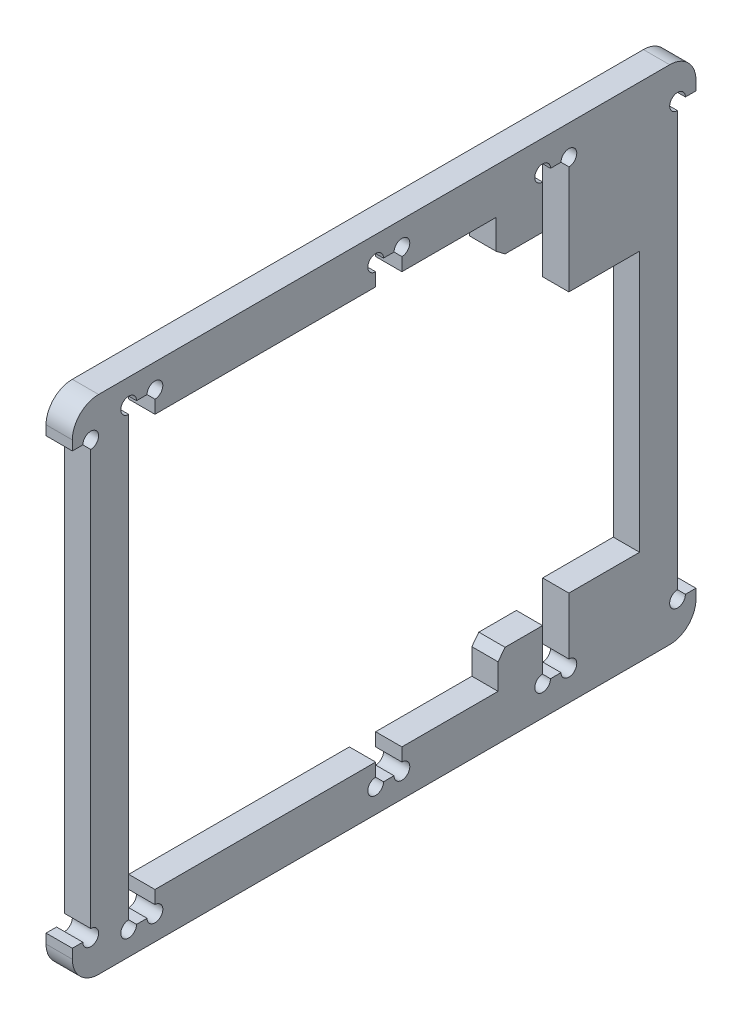
SolidWorks part; units mm, degrees
ref_plane "Front" through (0, 0, 0) normal (0, 0, 1) x (1, 0, 0)
ref_plane "Top" through (0, 0, 0) normal (0, 1, 0) x (1, 0, 0)
ref_plane "Right" through (0, 0, 0) normal (1, 0, 0) x (0, 0, -1)
sketch "Sketch1" plane through (0, 0, 0) normal (1, 0, 0) x (0, 0, -1)
  line L0 (0, 47.8186) -> (0, -47.8186) construction
  line L1 (-59.3692, -47.8186) -> (0, -47.8186)
  line L2 (-59.3692, -47.8186) -> (-59.3692, -41)
  line L3 (-59.3692, 47.8186) -> (59.3692, 47.8186)
  line L4 (59.3692, -47.8186) -> (59.3692, -41)
  line L5 (-59.3692, -47.8186) -> (59.3692, 47.8186) construction
  line L6 (-59.3692, 47.8186) -> (59.3692, -47.8186) construction
  line L7 (-70.2933, 0) -> (70.2933, 0) construction
  line L8 (30.1791, 39.1754) -> (48.6382, 39.1754) construction
  line L9 (30.1791, -39.1754) -> (48.6382, -39.1754) construction
  line L10 (21.7026, -39.1754) -> (21.7026, -34.307)
  line L11 (21.7026, -34.307) -> (23.0249, -32.5698)
  line L12 (23.0249, -32.5698) -> (30.1791, -32.5698)
  line L13 (21.2876, 39.1754) -> (21.2876, 33.6105)
  line L14 (-55.8692, -41) -> (-59.3692, -41)
  line L15 (-55.8692, -41) -> (-55.8692, 41)
  line L16 (0, -47.8186) -> (59.3692, -47.8186)
  line L17 (-55.8692, 41) -> (-59.3692, 41)
  line L18 (-55.8692, -41) -> (-59.3692, 41) construction
  line L19 (-59.3692, -41) -> (-55.8692, 41) construction
  line L20 (59.3692, -41) -> (55.8692, 41) construction
  line L21 (55.8692, -41) -> (59.3692, 41) construction
  line L22 (55.8692, 41) -> (59.3692, 41)
  line L23 (-59.3692, 41) -> (-59.3692, 47.8186)
  line L24 (55.8692, -41) -> (55.8692, 41)
  line L25 (55.8692, -41) -> (59.3692, -41)
  line L26 (59.3692, 41) -> (59.3692, 47.8186)
  line L27 (21.2876, 33.6105) -> (23.0249, 32.2882)
  line L28 (-48.6382, -39.1754) -> (-48.6382, 39.1754)
  line L29 (-48.6382, 39.1754) -> (21.2876, 39.1754)
  line L30 (48.6382, -29.7104) -> (48.6382, 19.9452)
  line L31 (-48.6382, -39.1754) -> (48.6382, 39.1754) construction
  line L32 (-48.6382, 39.1754) -> (48.6382, -39.1754) construction
  line L33 (30.1791, 39.1754) -> (21.2876, 39.1754) construction
  line L34 (35.1791, 19.9452) -> (35.1791, 42.077)
  line L35 (30.1791, 42.077) -> (30.1791, 32.2882)
  line L36 (30.1791, 42.077) -> (35.1791, 42.077)
  line L37 (35.1791, 19.9452) -> (48.6382, 19.9452)
  line L38 (21.7026, -39.1754) -> (-48.6382, -39.1754)
  line L39 (30.1791, -39.1754) -> (21.7026, -39.1754) construction
  line L40 (23.0249, 32.2882) -> (30.1791, 32.2882)
  line L41 (30.1791, -42.077) -> (35.1791, -42.077)
  line L42 (30.1791, -42.077) -> (30.1791, -32.5698)
  line L43 (35.1791, -29.7104) -> (35.1791, -42.077)
  line L44 (35.1791, -29.7104) -> (48.6382, -29.7104)
  line L46 (48.6382, 39.1754) -> (48.6382, 19.9452) construction
  line L47 (48.6382, -29.7104) -> (48.6382, -39.1754) construction
  point P0 (0, 0)
  point P12 (-57.6192, 0)
  point P24 (57.6192, 0)
  point P25 (0, 0)
  dimension "D1" = 3.5
  dimension "D2" = 82
  dimension "D3" = 5
extrude "Boss-Extrude1" add sketch "Sketch1" along normal blind 5
fillet "Fillet1" radius 5 4 edges at (2.5, 47.8186, 59.3692) (2.5, -47.8186, 59.3692) (2.5, -47.8186, -59.3692) (2.5, 47.8186, -59.3692)
sketch "Sketch2" plane through (0, 0, 0) normal (-1, 0, 0) x (0, 0, 1)
  line L0 (-23.2735, 0) -> (52.259, 0) construction
  line L1 (-3.3843, -43.1754) -> (1.6157, -43.1754)
  line L2 (-3.3843, -43.1754) -> (-3.3843, 43.1754)
  line L3 (-3.3843, 43.1754) -> (1.6157, 43.1754)
  line L4 (1.6157, -43.1754) -> (1.6157, 43.1754)
  line L5 (-3.3843, -43.1754) -> (1.6157, 43.1754) construction
  line L6 (-3.3843, 43.1754) -> (1.6157, -43.1754) construction
  line L7 (-21.2876, 39.1754) -> (48.6382, 39.1754) construction
  line L8 (43.6382, -43.1754) -> (48.6382, -43.1754)
  line L9 (43.6382, -43.1754) -> (43.6382, 43.1754)
  line L10 (43.6382, 43.1754) -> (48.6382, 43.1754)
  line L11 (48.6382, -43.1754) -> (48.6382, 43.1754)
  line L12 (43.6382, -43.1754) -> (48.6382, 43.1754) construction
  line L13 (43.6382, 43.1754) -> (48.6382, -43.1754) construction
  line L15 (48.6382, 39.1754) -> (48.6382, -39.1754) construction
  point P0 (-0.8843, 0)
  point P8 (46.1382, 0)
  line M18 (48.6382, -39.1754) -> (-21.7026, -39.1754)
  line M30 (-21.2876, 39.1754) -> (48.6382, 39.1754)
  dimension "D1" = 4
  dimension "D2" = 5
extrude "Cut-Extrude1" cut sketch "Sketch2" against normal up to next contours L11 L10 L9 M30 | L8 L11 L9 M18 | L1 L4 L2 M18 | L4 L3 L2 M30
sketch "Sketch3" plane through (0, 0, 0) normal (-1, 0, 0) x (0, 0, 1)
  line L1 (-55.8692, -41) -> (-55.8692, 41) construction
  circle A0 centre (-35.1791, 42.077) radius 1.5
  circle A1 centre (-30.1791, 42.077) radius 1.5
  circle A2 centre (-3.3843, 43.1754) radius 1.5
  circle A3 centre (1.6157, 43.1754) radius 1.5
  circle A4 centre (-55.8692, 41) radius 1.5
  circle A5 centre (43.6382, 43.1754) radius 1.5
  circle A6 centre (48.6382, 43.1754) radius 1.5
  circle A7 centre (48.6382, -43.1754) radius 1.5
  circle A8 centre (43.6382, -43.1754) radius 1.5
  circle A9 centre (1.6157, -43.1754) radius 1.5
  circle A10 centre (-3.3843, -43.1754) radius 1.5
  circle A11 centre (-30.1791, -42.077) radius 1.5
  circle A12 centre (-35.1791, -42.077) radius 1.5
  circle A13 centre (-55.8692, -41) radius 1.5
  circle A14 centre (55.8692, -41) radius 1.5
  circle A15 centre (55.8692, 41) radius 1.5
  dimension "D1" = 3
extrude "Cut-Extrude2" cut sketch "Sketch3" against normal up to next
ref_plane "Plane1" through (5, 40.577, -35.1791) normal (0, 0, -1) x (-1, 0, 0)
